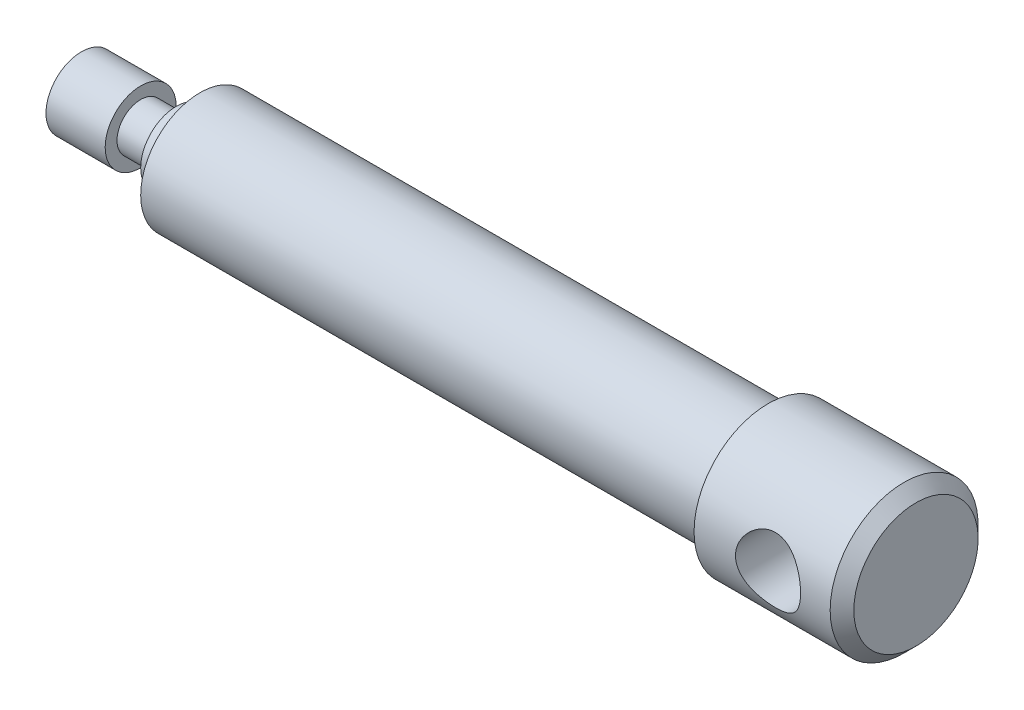
SolidWorks part; units mm, degrees
material "PBT General Purpose"
ref_plane "Front Plane" through (0, 0, 0) normal (0, 0, 1) x (1, 0, 0)
ref_plane "Top Plane" through (0, 0, 0) normal (0, 1, 0) x (1, 0, 0)
ref_plane "Right Plane" through (0, 0, 0) normal (1, 0, 0) x (0, 0, -1)
sketch "Sketch1" plane through (0, 0, 0) normal (0, 0, 1) x (1, 0, 0)
  line L0 (0, 0) -> (30.0117, 0) construction
  line L3 (3.4641, 6) -> (0, 0)
  line L4 (0, 0) -> (-5.8921, 0) construction
  line L5 (0, 0) -> (-3.5698, 6.1831) construction
  line L6 (0, 0) -> (-3.9897, -6.9103) construction
  line L7 (3.4641, 6) -> (13.4641, 6)
  line L8 (13.4641, 6) -> (13.4641, 4)
  line L9 (13.4641, 4) -> (19.4641, 4)
  line L10 (19.4641, 4) -> (19.4641, 6)
  line L11 (19.4641, 6) -> (23.4641, 6)
  line L12 (23.4641, 6) -> (23.4641, 10)
  line L13 (23.4641, 10) -> (119.4641, 10)
  line L14 (119.4641, 10) -> (119.4641, 12.5)
  line L15 (0, 0) -> (144.4641, 0)
  line L16 (119.4641, 12.5) -> (142.4641, 12.5)
  line L17 (144.4641, 10.5) -> (144.4641, 0)
  line L18 (142.4641, 12.5) -> (144.4641, 10.5)
  point P2 (142.8104, -0.5722)
  point P17 (99.0134, 0)
  point P18 (144.4641, 12.5)
  point P19 (143.9272, 0)
  point P21 (30.0117, 0)
  dimension "D1" = 120
  dimension "D2" = 6
  dimension "D3" = 10
  dimension "D4" = 6
  dimension "D5" = 4
  dimension "D6" = 4
  dimension "D7" = 10
  dimension "D8" = 12.5
  dimension "D9" = 60
  dimension "D10" = 25
  dimension "D11" = 121
  dimension "D12" = 2
  dimension "D13" = 45
revolve "Revolve1" add sketch "Sketch1" angle 360 about L15
sketch "Sketch2" plane through (0, 0, 0) normal (0, 0, 1) x (1, 0, 0)
  line L0 (144.4641, -10.5) -> (144.4641, 10.5) construction
  circle A0 centre (131.9641, 0) radius 5.5
  point P5 (0, 0)
  dimension "D1" = 12.5
  dimension "D2" = 11
extrude "Cut-Extrude1" cut sketch "Sketch2" along normal through all both and the other way through all
